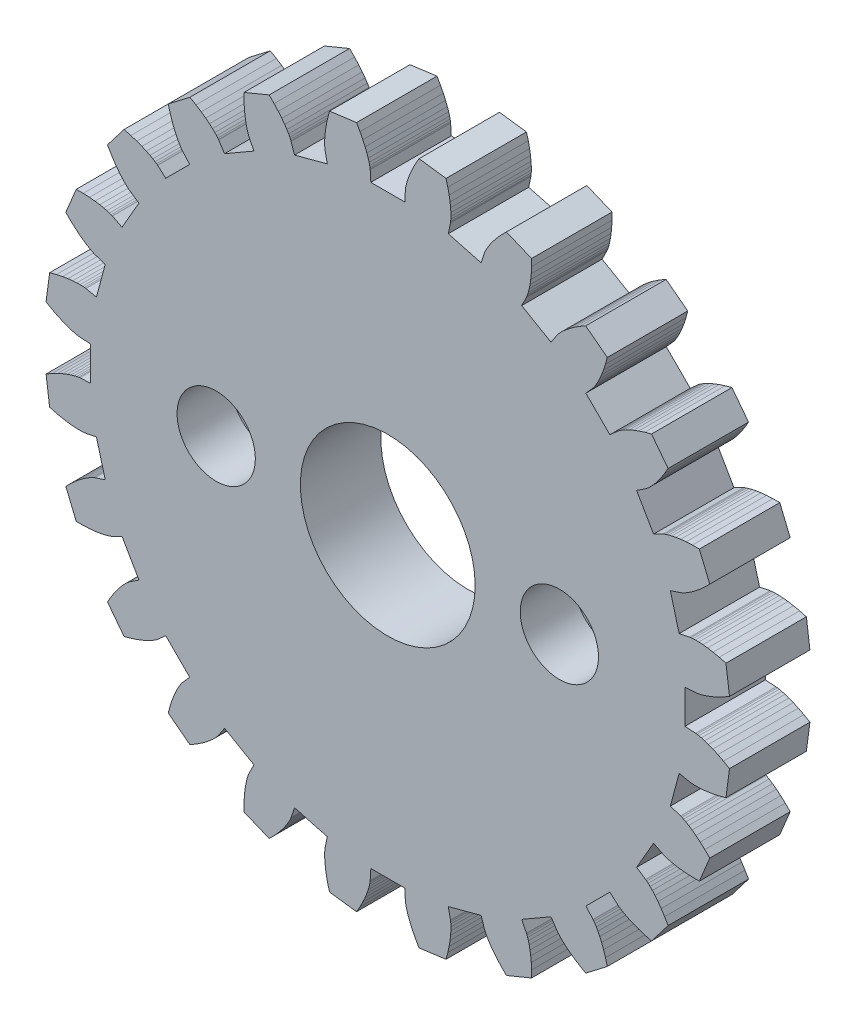
SolidWorks part; units mm, degrees
material "ABS"
ref_plane "Front Plane" through (0, 0, 0) normal (0, 0, 1) x (1, 0, 0)
ref_plane "Top Plane" through (0, 0, 0) normal (0, 1, 0) x (1, 0, 0)
ref_plane "Right Plane" through (0, 0, 0) normal (1, 0, 0) x (0, 0, -1)
sketch "Model" plane through (0, 0, 0) normal (0, 0, 1) x (1, 0, 0)
  line L0 (11.4813, -0.6559) -> (11.0819, -0.6331)
  line L1 (11.0819, -0.6331) -> (11.0819, 0.6331)
  line L2 (11.4813, 0.6559) -> (11.0819, 0.6331)
  line L3 (11.4813, 0.6559) -> (11.495, 0.6571)
  line L4 (11.495, 0.6571) -> (11.5358, 0.6626)
  line L5 (11.5358, 0.6626) -> (11.6033, 0.6749)
  line L6 (11.6033, 0.6749) -> (11.697, 0.6968)
  line L7 (11.697, 0.6968) -> (11.8158, 0.7307)
  line L8 (11.8158, 0.7307) -> (11.9589, 0.7792)
  line L9 (11.9589, 0.7792) -> (12.125, 0.8446)
  line L10 (12.125, 0.8446) -> (12.3128, 0.9294)
  line L11 (12.3128, 0.9294) -> (12.5206, 1.0358)
  line L12 (12.5206, 1.0358) -> (12.7468, 1.1658)
  line L13 (11.2598, 2.338) -> (11.2734, 2.3404)
  line L14 (11.2734, 2.3404) -> (11.3142, 2.3457)
  line L15 (11.3142, 2.3457) -> (11.3827, 2.3512)
  line L16 (11.3827, 2.3512) -> (11.4787, 2.3543)
  line L17 (11.4787, 2.3543) -> (11.6023, 2.3524)
  line L18 (11.6023, 2.3524) -> (11.7531, 2.3426)
  line L19 (11.7531, 2.3426) -> (11.9305, 2.3223)
  line L20 (11.9305, 2.3223) -> (12.1338, 2.289)
  line L21 (12.1338, 2.289) -> (12.362, 2.2401)
  line L22 (12.362, 2.2401) -> (12.6142, 2.173)
  line L23 (12.7468, 1.1658) -> (12.6142, 2.173)
  line L24 (11.2598, 2.338) -> (10.8682, 2.2567)
  line L25 (10.8682, 2.2567) -> (10.5405, 3.4797)
  line L26 (10.9203, 3.6051) -> (10.5405, 3.4797)
  line L27 (10.9203, 3.6051) -> (10.9332, 3.6098)
  line L28 (10.9332, 3.6098) -> (10.9712, 3.6257)
  line L29 (10.9712, 3.6257) -> (11.0333, 3.6551)
  line L30 (11.0333, 3.6551) -> (11.1181, 3.7004)
  line L31 (11.1181, 3.7004) -> (11.2241, 3.764)
  line L32 (11.2241, 3.764) -> (11.3497, 3.8478)
  line L33 (11.3497, 3.8478) -> (11.4933, 3.954)
  line L34 (11.4933, 3.954) -> (11.6527, 4.0845)
  line L35 (11.6527, 4.0845) -> (11.8259, 4.241)
  line L36 (11.8259, 4.241) -> (12.0107, 4.4252)
  line L37 (10.271, 5.1726) -> (10.2835, 5.1784)
  line L38 (10.2835, 5.1784) -> (10.3216, 5.1941)
  line L39 (10.3216, 5.1941) -> (10.3863, 5.2172)
  line L40 (10.3863, 5.2172) -> (10.4783, 5.245)
  line L41 (10.4783, 5.245) -> (10.5981, 5.2751)
  line L42 (10.5981, 5.2751) -> (10.7463, 5.3047)
  line L43 (10.7463, 5.3047) -> (10.9229, 5.331)
  line L44 (10.9229, 5.331) -> (11.1279, 5.3515)
  line L45 (11.1279, 5.3515) -> (11.361, 5.3633)
  line L46 (11.361, 5.3633) -> (11.622, 5.3638)
  line L47 (12.0107, 4.4252) -> (11.622, 5.3638)
  line L48 (10.271, 5.1726) -> (9.9138, 4.9927)
  line L49 (9.9138, 4.9927) -> (9.2807, 6.0892)
  line L50 (9.6151, 6.3087) -> (9.2807, 6.0892)
  line L51 (9.6151, 6.3087) -> (9.6264, 6.3166)
  line L52 (9.6264, 6.3166) -> (9.659, 6.3417)
  line L53 (9.659, 6.3417) -> (9.7113, 6.3862)
  line L54 (9.7113, 6.3862) -> (9.7815, 6.4519)
  line L55 (9.7815, 6.4519) -> (9.8675, 6.5407)
  line L56 (9.8675, 6.5407) -> (9.9671, 6.6542)
  line L57 (9.9671, 6.6542) -> (10.0783, 6.794)
  line L58 (10.0783, 6.794) -> (10.1985, 6.9613)
  line L59 (10.1985, 6.9613) -> (10.3253, 7.1573)
  line L60 (10.3253, 7.1573) -> (10.4561, 7.383)
  line L61 (8.5823, 7.6547) -> (8.5928, 7.6635)
  line L62 (8.5928, 7.6635) -> (8.6256, 7.6885)
  line L63 (8.6256, 7.6885) -> (8.6821, 7.7275)
  line L64 (8.6821, 7.7275) -> (8.7637, 7.7783)
  line L65 (8.7637, 7.7783) -> (8.8717, 7.8384)
  line L66 (8.8717, 7.8384) -> (9.0072, 7.9053)
  line L67 (9.0072, 7.9053) -> (9.1709, 7.9764)
  line L68 (9.1709, 7.9764) -> (9.3636, 8.0492)
  line L69 (9.3636, 8.0492) -> (9.5858, 8.121)
  line L70 (9.5858, 8.121) -> (9.8377, 8.189)
  line L71 (10.4561, 7.383) -> (9.8377, 8.189)
  line L72 (8.5823, 7.6547) -> (8.2838, 7.3885)
  line L73 (8.2838, 7.3885) -> (7.3885, 8.2838)
  line L74 (7.6547, 8.5823) -> (7.3885, 8.2838)
  line L75 (7.6547, 8.5823) -> (7.6635, 8.5928)
  line L76 (7.6635, 8.5928) -> (7.6885, 8.6256)
  line L77 (7.6885, 8.6256) -> (7.7275, 8.6821)
  line L78 (7.7275, 8.6821) -> (7.7783, 8.7637)
  line L79 (7.7783, 8.7637) -> (7.8384, 8.8717)
  line L80 (7.8384, 8.8717) -> (7.9053, 9.0072)
  line L81 (7.9053, 9.0072) -> (7.9764, 9.1709)
  line L82 (7.9764, 9.1709) -> (8.0492, 9.3636)
  line L83 (8.0492, 9.3636) -> (8.121, 9.5858)
  line L84 (8.121, 9.5858) -> (8.189, 9.8377)
  line L85 (6.3087, 9.6151) -> (6.3166, 9.6264)
  line L86 (6.3166, 9.6264) -> (6.3417, 9.659)
  line L87 (6.3417, 9.659) -> (6.3862, 9.7113)
  line L88 (6.3862, 9.7113) -> (6.4519, 9.7815)
  line L89 (6.4519, 9.7815) -> (6.5407, 9.8675)
  line L90 (6.5407, 9.8675) -> (6.6542, 9.9671)
  line L91 (6.6542, 9.9671) -> (6.794, 10.0783)
  line L92 (6.794, 10.0783) -> (6.9613, 10.1985)
  line L93 (6.9613, 10.1985) -> (7.1573, 10.3253)
  line L94 (7.1573, 10.3253) -> (7.383, 10.4561)
  line L95 (8.189, 9.8377) -> (7.383, 10.4561)
  line L96 (6.3087, 9.6151) -> (6.0892, 9.2807)
  line L97 (6.0892, 9.2807) -> (4.9927, 9.9138)
  line L98 (5.1726, 10.271) -> (4.9927, 9.9138)
  line L99 (5.1726, 10.271) -> (5.1784, 10.2835)
  line L100 (5.1784, 10.2835) -> (5.1941, 10.3216)
  line L101 (5.1941, 10.3216) -> (5.2172, 10.3863)
  line L102 (5.2172, 10.3863) -> (5.245, 10.4783)
  line L103 (5.245, 10.4783) -> (5.2751, 10.5981)
  line L104 (5.2751, 10.5981) -> (5.3047, 10.7463)
  line L105 (5.3047, 10.7463) -> (5.331, 10.9229)
  line L106 (5.331, 10.9229) -> (5.3515, 11.1279)
  line L107 (5.3515, 11.1279) -> (5.3633, 11.361)
  line L108 (5.3633, 11.361) -> (5.3638, 11.622)
  line L109 (3.6051, 10.9203) -> (3.6098, 10.9332)
  line L110 (3.6098, 10.9332) -> (3.6257, 10.9712)
  line L111 (3.6257, 10.9712) -> (3.6551, 11.0333)
  line L112 (3.6551, 11.0333) -> (3.7004, 11.1181)
  line L113 (3.7004, 11.1181) -> (3.764, 11.2241)
  line L114 (3.764, 11.2241) -> (3.8478, 11.3497)
  line L115 (3.8478, 11.3497) -> (3.954, 11.4933)
  line L116 (3.954, 11.4933) -> (4.0845, 11.6527)
  line L117 (4.0845, 11.6527) -> (4.241, 11.8259)
  line L118 (4.241, 11.8259) -> (4.4252, 12.0107)
  line L119 (5.3638, 11.622) -> (4.4252, 12.0107)
  line L120 (3.6051, 10.9203) -> (3.4797, 10.5405)
  line L121 (3.4797, 10.5405) -> (2.2567, 10.8682)
  line L122 (2.338, 11.2598) -> (2.2567, 10.8682)
  line L123 (2.338, 11.2598) -> (2.3404, 11.2734)
  line L124 (2.3404, 11.2734) -> (2.3457, 11.3142)
  line L125 (2.3457, 11.3142) -> (2.3512, 11.3827)
  line L126 (2.3512, 11.3827) -> (2.3543, 11.4787)
  line L127 (2.3543, 11.4787) -> (2.3524, 11.6023)
  line L128 (2.3524, 11.6023) -> (2.3426, 11.7531)
  line L129 (2.3426, 11.7531) -> (2.3223, 11.9305)
  line L130 (2.3223, 11.9305) -> (2.289, 12.1338)
  line L131 (2.289, 12.1338) -> (2.2401, 12.362)
  line L132 (2.2401, 12.362) -> (2.173, 12.6142)
  line L133 (0.6559, 11.4813) -> (0.6571, 11.495)
  line L134 (0.6571, 11.495) -> (0.6626, 11.5358)
  line L135 (0.6626, 11.5358) -> (0.6749, 11.6033)
  line L136 (0.6749, 11.6033) -> (0.6968, 11.697)
  line L137 (0.6968, 11.697) -> (0.7307, 11.8158)
  line L138 (0.7307, 11.8158) -> (0.7792, 11.9589)
  line L139 (0.7792, 11.9589) -> (0.8446, 12.125)
  line L140 (0.8446, 12.125) -> (0.9294, 12.3128)
  line L141 (0.9294, 12.3128) -> (1.0358, 12.5206)
  line L142 (1.0358, 12.5206) -> (1.1658, 12.7468)
  line L143 (2.173, 12.6142) -> (1.1658, 12.7468)
  line L144 (0.6559, 11.4813) -> (0.6331, 11.0819)
  line L145 (0.6331, 11.0819) -> (-0.6331, 11.0819)
  line L146 (-0.6559, 11.4813) -> (-0.6331, 11.0819)
  line L147 (-0.6559, 11.4813) -> (-0.6571, 11.495)
  line L148 (-0.6571, 11.495) -> (-0.6626, 11.5358)
  line L149 (-0.6626, 11.5358) -> (-0.6749, 11.6033)
  line L150 (-0.6749, 11.6033) -> (-0.6968, 11.697)
  line L151 (-0.6968, 11.697) -> (-0.7307, 11.8158)
  line L152 (-0.7307, 11.8158) -> (-0.7792, 11.9589)
  line L153 (-0.7792, 11.9589) -> (-0.8446, 12.125)
  line L154 (-0.8446, 12.125) -> (-0.9294, 12.3128)
  line L155 (-0.9294, 12.3128) -> (-1.0358, 12.5206)
  line L156 (-1.0358, 12.5206) -> (-1.1658, 12.7468)
  line L157 (-2.338, 11.2598) -> (-2.3404, 11.2734)
  line L158 (-2.3404, 11.2734) -> (-2.3457, 11.3142)
  line L159 (-2.3457, 11.3142) -> (-2.3512, 11.3827)
  line L160 (-2.3512, 11.3827) -> (-2.3543, 11.4787)
  line L161 (-2.3543, 11.4787) -> (-2.3524, 11.6023)
  line L162 (-2.3524, 11.6023) -> (-2.3426, 11.7531)
  line L163 (-2.3426, 11.7531) -> (-2.3223, 11.9305)
  line L164 (-2.3223, 11.9305) -> (-2.289, 12.1338)
  line L165 (-2.289, 12.1338) -> (-2.2401, 12.362)
  line L166 (-2.2401, 12.362) -> (-2.173, 12.6142)
  line L167 (-1.1658, 12.7468) -> (-2.173, 12.6142)
  line L168 (-2.338, 11.2598) -> (-2.2567, 10.8682)
  line L169 (-2.2567, 10.8682) -> (-3.4797, 10.5405)
  line L170 (-3.6051, 10.9203) -> (-3.4797, 10.5405)
  line L171 (-3.6051, 10.9203) -> (-3.6098, 10.9332)
  line L172 (-3.6098, 10.9332) -> (-3.6257, 10.9712)
  line L173 (-3.6257, 10.9712) -> (-3.6551, 11.0333)
  line L174 (-3.6551, 11.0333) -> (-3.7004, 11.1181)
  line L175 (-3.7004, 11.1181) -> (-3.764, 11.2241)
  line L176 (-3.764, 11.2241) -> (-3.8478, 11.3497)
  line L177 (-3.8478, 11.3497) -> (-3.954, 11.4933)
  line L178 (-3.954, 11.4933) -> (-4.0845, 11.6527)
  line L179 (-4.0845, 11.6527) -> (-4.241, 11.8259)
  line L180 (-4.241, 11.8259) -> (-4.4252, 12.0107)
  line L181 (-5.1726, 10.271) -> (-5.1784, 10.2835)
  line L182 (-5.1784, 10.2835) -> (-5.1941, 10.3216)
  line L183 (-5.1941, 10.3216) -> (-5.2172, 10.3863)
  line L184 (-5.2172, 10.3863) -> (-5.245, 10.4783)
  line L185 (-5.245, 10.4783) -> (-5.2751, 10.5981)
  line L186 (-5.2751, 10.5981) -> (-5.3047, 10.7463)
  line L187 (-5.3047, 10.7463) -> (-5.331, 10.9229)
  line L188 (-5.331, 10.9229) -> (-5.3515, 11.1279)
  line L189 (-5.3515, 11.1279) -> (-5.3633, 11.361)
  line L190 (-5.3633, 11.361) -> (-5.3638, 11.622)
  line L191 (-4.4252, 12.0107) -> (-5.3638, 11.622)
  line L192 (-5.1726, 10.271) -> (-4.9927, 9.9138)
  line L193 (-4.9927, 9.9138) -> (-6.0892, 9.2807)
  line L194 (-6.3087, 9.6151) -> (-6.0892, 9.2807)
  line L195 (-6.3087, 9.6151) -> (-6.3166, 9.6264)
  line L196 (-6.3166, 9.6264) -> (-6.3417, 9.659)
  line L197 (-6.3417, 9.659) -> (-6.3862, 9.7113)
  line L198 (-6.3862, 9.7113) -> (-6.4519, 9.7815)
  line L199 (-6.4519, 9.7815) -> (-6.5407, 9.8675)
  line L200 (-6.5407, 9.8675) -> (-6.6542, 9.9671)
  line L201 (-6.6542, 9.9671) -> (-6.794, 10.0783)
  line L202 (-6.794, 10.0783) -> (-6.9613, 10.1985)
  line L203 (-6.9613, 10.1985) -> (-7.1573, 10.3253)
  line L204 (-7.1573, 10.3253) -> (-7.383, 10.4561)
  line L205 (-7.6547, 8.5823) -> (-7.6635, 8.5928)
  line L206 (-7.6635, 8.5928) -> (-7.6885, 8.6256)
  line L207 (-7.6885, 8.6256) -> (-7.7275, 8.6821)
  line L208 (-7.7275, 8.6821) -> (-7.7783, 8.7637)
  line L209 (-7.7783, 8.7637) -> (-7.8384, 8.8717)
  line L210 (-7.8384, 8.8717) -> (-7.9053, 9.0072)
  line L211 (-7.9053, 9.0072) -> (-7.9764, 9.1709)
  line L212 (-7.9764, 9.1709) -> (-8.0492, 9.3636)
  line L213 (-8.0492, 9.3636) -> (-8.121, 9.5858)
  line L214 (-8.121, 9.5858) -> (-8.189, 9.8377)
  line L215 (-7.383, 10.4561) -> (-8.189, 9.8377)
  line L216 (-7.6547, 8.5823) -> (-7.3885, 8.2838)
  line L217 (-7.3885, 8.2838) -> (-8.2838, 7.3885)
  line L218 (-8.5823, 7.6547) -> (-8.2838, 7.3885)
  line L219 (-8.5823, 7.6547) -> (-8.5928, 7.6635)
  line L220 (-8.5928, 7.6635) -> (-8.6256, 7.6885)
  line L221 (-8.6256, 7.6885) -> (-8.6821, 7.7275)
  line L222 (-8.6821, 7.7275) -> (-8.7637, 7.7783)
  line L223 (-8.7637, 7.7783) -> (-8.8717, 7.8384)
  line L224 (-8.8717, 7.8384) -> (-9.0072, 7.9053)
  line L225 (-9.0072, 7.9053) -> (-9.1709, 7.9764)
  line L226 (-9.1709, 7.9764) -> (-9.3636, 8.0492)
  line L227 (-9.3636, 8.0492) -> (-9.5858, 8.121)
  line L228 (-9.5858, 8.121) -> (-9.8377, 8.189)
  line L229 (-9.6151, 6.3087) -> (-9.6264, 6.3166)
  line L230 (-9.6264, 6.3166) -> (-9.659, 6.3417)
  line L231 (-9.659, 6.3417) -> (-9.7113, 6.3862)
  line L232 (-9.7113, 6.3862) -> (-9.7815, 6.4519)
  line L233 (-9.7815, 6.4519) -> (-9.8675, 6.5407)
  line L234 (-9.8675, 6.5407) -> (-9.9671, 6.6542)
  line L235 (-9.9671, 6.6542) -> (-10.0783, 6.794)
  line L236 (-10.0783, 6.794) -> (-10.1985, 6.9613)
  line L237 (-10.1985, 6.9613) -> (-10.3253, 7.1573)
  line L238 (-10.3253, 7.1573) -> (-10.4561, 7.383)
  line L239 (-9.8377, 8.189) -> (-10.4561, 7.383)
  line L240 (-9.6151, 6.3087) -> (-9.2807, 6.0892)
  line L241 (-9.2807, 6.0892) -> (-9.9138, 4.9927)
  line L242 (-10.271, 5.1726) -> (-9.9138, 4.9927)
  line L243 (-10.271, 5.1726) -> (-10.2835, 5.1784)
  line L244 (-10.2835, 5.1784) -> (-10.3216, 5.1941)
  line L245 (-10.3216, 5.1941) -> (-10.3863, 5.2172)
  line L246 (-10.3863, 5.2172) -> (-10.4783, 5.245)
  line L247 (-10.4783, 5.245) -> (-10.5981, 5.2751)
  line L248 (-10.5981, 5.2751) -> (-10.7463, 5.3047)
  line L249 (-10.7463, 5.3047) -> (-10.9229, 5.331)
  line L250 (-10.9229, 5.331) -> (-11.1279, 5.3515)
  line L251 (-11.1279, 5.3515) -> (-11.361, 5.3633)
  line L252 (-11.361, 5.3633) -> (-11.622, 5.3638)
  line L253 (-10.9203, 3.6051) -> (-10.9332, 3.6098)
  line L254 (-10.9332, 3.6098) -> (-10.9712, 3.6257)
  line L255 (-10.9712, 3.6257) -> (-11.0333, 3.6551)
  line L256 (-11.0333, 3.6551) -> (-11.1181, 3.7004)
  line L257 (-11.1181, 3.7004) -> (-11.2241, 3.764)
  line L258 (-11.2241, 3.764) -> (-11.3497, 3.8478)
  line L259 (-11.3497, 3.8478) -> (-11.4933, 3.954)
  line L260 (-11.4933, 3.954) -> (-11.6527, 4.0845)
  line L261 (-11.6527, 4.0845) -> (-11.8259, 4.241)
  line L262 (-11.8259, 4.241) -> (-12.0107, 4.4252)
  line L263 (-11.622, 5.3638) -> (-12.0107, 4.4252)
  line L264 (-10.9203, 3.6051) -> (-10.5405, 3.4797)
  line L265 (-10.5405, 3.4797) -> (-10.8682, 2.2567)
  line L266 (-11.2598, 2.338) -> (-10.8682, 2.2567)
  line L267 (-11.2598, 2.338) -> (-11.2734, 2.3404)
  line L268 (-11.2734, 2.3404) -> (-11.3142, 2.3457)
  line L269 (-11.3142, 2.3457) -> (-11.3827, 2.3512)
  line L270 (-11.3827, 2.3512) -> (-11.4787, 2.3543)
  line L271 (-11.4787, 2.3543) -> (-11.6023, 2.3524)
  line L272 (-11.6023, 2.3524) -> (-11.7531, 2.3426)
  line L273 (-11.7531, 2.3426) -> (-11.9305, 2.3223)
  line L274 (-11.9305, 2.3223) -> (-12.1338, 2.289)
  line L275 (-12.1338, 2.289) -> (-12.362, 2.2401)
  line L276 (-12.362, 2.2401) -> (-12.6142, 2.173)
  line L277 (-11.4813, 0.6559) -> (-11.495, 0.6571)
  line L278 (-11.495, 0.6571) -> (-11.5358, 0.6626)
  line L279 (-11.5358, 0.6626) -> (-11.6033, 0.6749)
  line L280 (-11.6033, 0.6749) -> (-11.697, 0.6968)
  line L281 (-11.697, 0.6968) -> (-11.8158, 0.7307)
  line L282 (-11.8158, 0.7307) -> (-11.9589, 0.7792)
  line L283 (-11.9589, 0.7792) -> (-12.125, 0.8446)
  line L284 (-12.125, 0.8446) -> (-12.3128, 0.9294)
  line L285 (-12.3128, 0.9294) -> (-12.5206, 1.0358)
  line L286 (-12.5206, 1.0358) -> (-12.7468, 1.1658)
  line L287 (-12.6142, 2.173) -> (-12.7468, 1.1658)
  line L288 (-11.4813, 0.6559) -> (-11.0819, 0.6331)
  line L289 (-11.0819, 0.6331) -> (-11.0819, -0.6331)
  line L290 (-11.4813, -0.6559) -> (-11.0819, -0.6331)
  line L291 (-11.4813, -0.6559) -> (-11.495, -0.6571)
  line L292 (-11.495, -0.6571) -> (-11.5358, -0.6626)
  line L293 (-11.5358, -0.6626) -> (-11.6033, -0.6749)
  line L294 (-11.6033, -0.6749) -> (-11.697, -0.6968)
  line L295 (-11.697, -0.6968) -> (-11.8158, -0.7307)
  line L296 (-11.8158, -0.7307) -> (-11.9589, -0.7792)
  line L297 (-11.9589, -0.7792) -> (-12.125, -0.8446)
  line L298 (-12.125, -0.8446) -> (-12.3128, -0.9294)
  line L299 (-12.3128, -0.9294) -> (-12.5206, -1.0358)
  line L300 (-12.5206, -1.0358) -> (-12.7468, -1.1658)
  line L301 (-11.2598, -2.338) -> (-11.2734, -2.3404)
  line L302 (-11.2734, -2.3404) -> (-11.3142, -2.3457)
  line L303 (-11.3142, -2.3457) -> (-11.3827, -2.3512)
  line L304 (-11.3827, -2.3512) -> (-11.4787, -2.3543)
  line L305 (-11.4787, -2.3543) -> (-11.6023, -2.3524)
  line L306 (-11.6023, -2.3524) -> (-11.7531, -2.3426)
  line L307 (-11.7531, -2.3426) -> (-11.9305, -2.3223)
  line L308 (-11.9305, -2.3223) -> (-12.1338, -2.289)
  line L309 (-12.1338, -2.289) -> (-12.362, -2.2401)
  line L310 (-12.362, -2.2401) -> (-12.6142, -2.173)
  line L311 (-12.7468, -1.1658) -> (-12.6142, -2.173)
  line L312 (-11.2598, -2.338) -> (-10.8682, -2.2567)
  line L313 (-10.8682, -2.2567) -> (-10.5405, -3.4797)
  line L314 (-10.9203, -3.6051) -> (-10.5405, -3.4797)
  line L315 (-10.9203, -3.6051) -> (-10.9332, -3.6098)
  line L316 (-10.9332, -3.6098) -> (-10.9712, -3.6257)
  line L317 (-10.9712, -3.6257) -> (-11.0333, -3.6551)
  line L318 (-11.0333, -3.6551) -> (-11.1181, -3.7004)
  line L319 (-11.1181, -3.7004) -> (-11.2241, -3.764)
  line L320 (-11.2241, -3.764) -> (-11.3497, -3.8478)
  line L321 (-11.3497, -3.8478) -> (-11.4933, -3.954)
  line L322 (-11.4933, -3.954) -> (-11.6527, -4.0845)
  line L323 (-11.6527, -4.0845) -> (-11.8259, -4.241)
  line L324 (-11.8259, -4.241) -> (-12.0107, -4.4252)
  line L325 (-10.271, -5.1726) -> (-10.2835, -5.1784)
  line L326 (-10.2835, -5.1784) -> (-10.3216, -5.1941)
  line L327 (-10.3216, -5.1941) -> (-10.3863, -5.2172)
  line L328 (-10.3863, -5.2172) -> (-10.4783, -5.245)
  line L329 (-10.4783, -5.245) -> (-10.5981, -5.2751)
  line L330 (-10.5981, -5.2751) -> (-10.7463, -5.3047)
  line L331 (-10.7463, -5.3047) -> (-10.9229, -5.331)
  line L332 (-10.9229, -5.331) -> (-11.1279, -5.3515)
  line L333 (-11.1279, -5.3515) -> (-11.361, -5.3633)
  line L334 (-11.361, -5.3633) -> (-11.622, -5.3638)
  line L335 (-12.0107, -4.4252) -> (-11.622, -5.3638)
  line L336 (-10.271, -5.1726) -> (-9.9138, -4.9927)
  line L337 (-9.9138, -4.9927) -> (-9.2807, -6.0892)
  line L338 (-9.6151, -6.3087) -> (-9.2807, -6.0892)
  line L339 (-9.6151, -6.3087) -> (-9.6264, -6.3166)
  line L340 (-9.6264, -6.3166) -> (-9.659, -6.3417)
  line L341 (-9.659, -6.3417) -> (-9.7113, -6.3862)
  line L342 (-9.7113, -6.3862) -> (-9.7815, -6.4519)
  line L343 (-9.7815, -6.4519) -> (-9.8675, -6.5407)
  line L344 (-9.8675, -6.5407) -> (-9.9671, -6.6542)
  line L345 (-9.9671, -6.6542) -> (-10.0783, -6.794)
  line L346 (-10.0783, -6.794) -> (-10.1985, -6.9613)
  line L347 (-10.1985, -6.9613) -> (-10.3253, -7.1573)
  line L348 (-10.3253, -7.1573) -> (-10.4561, -7.383)
  line L349 (-8.5823, -7.6547) -> (-8.5928, -7.6635)
  line L350 (-8.5928, -7.6635) -> (-8.6256, -7.6885)
  line L351 (-8.6256, -7.6885) -> (-8.6821, -7.7275)
  line L352 (-8.6821, -7.7275) -> (-8.7637, -7.7783)
  line L353 (-8.7637, -7.7783) -> (-8.8717, -7.8384)
  line L354 (-8.8717, -7.8384) -> (-9.0072, -7.9053)
  line L355 (-9.0072, -7.9053) -> (-9.1709, -7.9764)
  line L356 (-9.1709, -7.9764) -> (-9.3636, -8.0492)
  line L357 (-9.3636, -8.0492) -> (-9.5858, -8.121)
  line L358 (-9.5858, -8.121) -> (-9.8377, -8.189)
  line L359 (-10.4561, -7.383) -> (-9.8377, -8.189)
  line L360 (-8.5823, -7.6547) -> (-8.2838, -7.3885)
  line L361 (-8.2838, -7.3885) -> (-7.3885, -8.2838)
  line L362 (-7.6547, -8.5823) -> (-7.3885, -8.2838)
  line L363 (-7.6547, -8.5823) -> (-7.6635, -8.5928)
  line L364 (-7.6635, -8.5928) -> (-7.6885, -8.6256)
  line L365 (-7.6885, -8.6256) -> (-7.7275, -8.6821)
  line L366 (-7.7275, -8.6821) -> (-7.7783, -8.7637)
  line L367 (-7.7783, -8.7637) -> (-7.8384, -8.8717)
  line L368 (-7.8384, -8.8717) -> (-7.9053, -9.0072)
  line L369 (-7.9053, -9.0072) -> (-7.9764, -9.1709)
  line L370 (-7.9764, -9.1709) -> (-8.0492, -9.3636)
  line L371 (-8.0492, -9.3636) -> (-8.121, -9.5858)
  line L372 (-8.121, -9.5858) -> (-8.189, -9.8377)
  line L373 (-6.3087, -9.6151) -> (-6.3166, -9.6264)
  line L374 (-6.3166, -9.6264) -> (-6.3417, -9.659)
  line L375 (-6.3417, -9.659) -> (-6.3862, -9.7113)
  line L376 (-6.3862, -9.7113) -> (-6.4519, -9.7815)
  line L377 (-6.4519, -9.7815) -> (-6.5407, -9.8675)
  line L378 (-6.5407, -9.8675) -> (-6.6542, -9.9671)
  line L379 (-6.6542, -9.9671) -> (-6.794, -10.0783)
  line L380 (-6.794, -10.0783) -> (-6.9613, -10.1985)
  line L381 (-6.9613, -10.1985) -> (-7.1573, -10.3253)
  line L382 (-7.1573, -10.3253) -> (-7.383, -10.4561)
  line L383 (-8.189, -9.8377) -> (-7.383, -10.4561)
  line L384 (-6.3087, -9.6151) -> (-6.0892, -9.2807)
  line L385 (-6.0892, -9.2807) -> (-4.9927, -9.9138)
  line L386 (-5.1726, -10.271) -> (-4.9927, -9.9138)
  line L387 (-5.1726, -10.271) -> (-5.1784, -10.2835)
  line L388 (-5.1784, -10.2835) -> (-5.1941, -10.3216)
  line L389 (-5.1941, -10.3216) -> (-5.2172, -10.3863)
  line L390 (-5.2172, -10.3863) -> (-5.245, -10.4783)
  line L391 (-5.245, -10.4783) -> (-5.2751, -10.5981)
  line L392 (-5.2751, -10.5981) -> (-5.3047, -10.7463)
  line L393 (-5.3047, -10.7463) -> (-5.331, -10.9229)
  line L394 (-5.331, -10.9229) -> (-5.3515, -11.1279)
  line L395 (-5.3515, -11.1279) -> (-5.3633, -11.361)
  line L396 (-5.3633, -11.361) -> (-5.3638, -11.622)
  line L397 (-3.6051, -10.9203) -> (-3.6098, -10.9332)
  line L398 (-3.6098, -10.9332) -> (-3.6257, -10.9712)
  line L399 (-3.6257, -10.9712) -> (-3.6551, -11.0333)
  line L400 (-3.6551, -11.0333) -> (-3.7004, -11.1181)
  line L401 (-3.7004, -11.1181) -> (-3.764, -11.2241)
  line L402 (-3.764, -11.2241) -> (-3.8478, -11.3497)
  line L403 (-3.8478, -11.3497) -> (-3.954, -11.4933)
  line L404 (-3.954, -11.4933) -> (-4.0845, -11.6527)
  line L405 (-4.0845, -11.6527) -> (-4.241, -11.8259)
  line L406 (-4.241, -11.8259) -> (-4.4252, -12.0107)
  line L407 (-5.3638, -11.622) -> (-4.4252, -12.0107)
  line L408 (-3.6051, -10.9203) -> (-3.4797, -10.5405)
  line L409 (-3.4797, -10.5405) -> (-2.2567, -10.8682)
  line L410 (-2.338, -11.2598) -> (-2.2567, -10.8682)
  line L411 (-2.338, -11.2598) -> (-2.3404, -11.2734)
  line L412 (-2.3404, -11.2734) -> (-2.3457, -11.3142)
  line L413 (-2.3457, -11.3142) -> (-2.3512, -11.3827)
  line L414 (-2.3512, -11.3827) -> (-2.3543, -11.4787)
  line L415 (-2.3543, -11.4787) -> (-2.3524, -11.6023)
  line L416 (-2.3524, -11.6023) -> (-2.3426, -11.7531)
  line L417 (-2.3426, -11.7531) -> (-2.3223, -11.9305)
  line L418 (-2.3223, -11.9305) -> (-2.289, -12.1338)
  line L419 (-2.289, -12.1338) -> (-2.2401, -12.362)
  line L420 (-2.2401, -12.362) -> (-2.173, -12.6142)
  line L421 (-0.6559, -11.4813) -> (-0.6571, -11.495)
  line L422 (-0.6571, -11.495) -> (-0.6626, -11.5358)
  line L423 (-0.6626, -11.5358) -> (-0.6749, -11.6033)
  line L424 (-0.6749, -11.6033) -> (-0.6968, -11.697)
  line L425 (-0.6968, -11.697) -> (-0.7307, -11.8158)
  line L426 (-0.7307, -11.8158) -> (-0.7792, -11.9589)
  line L427 (-0.7792, -11.9589) -> (-0.8446, -12.125)
  line L428 (-0.8446, -12.125) -> (-0.9294, -12.3128)
  line L429 (-0.9294, -12.3128) -> (-1.0358, -12.5206)
  line L430 (-1.0358, -12.5206) -> (-1.1658, -12.7468)
  line L431 (-2.173, -12.6142) -> (-1.1658, -12.7468)
  line L432 (-0.6559, -11.4813) -> (-0.6331, -11.0819)
  line L433 (-0.6331, -11.0819) -> (0.6331, -11.0819)
  line L434 (0.6559, -11.4813) -> (0.6331, -11.0819)
  line L435 (0.6559, -11.4813) -> (0.6571, -11.495)
  line L436 (0.6571, -11.495) -> (0.6626, -11.5358)
  line L437 (0.6626, -11.5358) -> (0.6749, -11.6033)
  line L438 (0.6749, -11.6033) -> (0.6968, -11.697)
  line L439 (0.6968, -11.697) -> (0.7307, -11.8158)
  line L440 (0.7307, -11.8158) -> (0.7792, -11.9589)
  line L441 (0.7792, -11.9589) -> (0.8446, -12.125)
  line L442 (0.8446, -12.125) -> (0.9294, -12.3128)
  line L443 (0.9294, -12.3128) -> (1.0358, -12.5206)
  line L444 (1.0358, -12.5206) -> (1.1658, -12.7468)
  line L445 (2.338, -11.2598) -> (2.3404, -11.2734)
  line L446 (2.3404, -11.2734) -> (2.3457, -11.3142)
  line L447 (2.3457, -11.3142) -> (2.3512, -11.3827)
  line L448 (2.3512, -11.3827) -> (2.3543, -11.4787)
  line L449 (2.3543, -11.4787) -> (2.3524, -11.6023)
  line L450 (2.3524, -11.6023) -> (2.3426, -11.7531)
  line L451 (2.3426, -11.7531) -> (2.3223, -11.9305)
  line L452 (2.3223, -11.9305) -> (2.289, -12.1338)
  line L453 (2.289, -12.1338) -> (2.2401, -12.362)
  line L454 (2.2401, -12.362) -> (2.173, -12.6142)
  line L455 (1.1658, -12.7468) -> (2.173, -12.6142)
  line L456 (2.338, -11.2598) -> (2.2567, -10.8682)
  line L457 (2.2567, -10.8682) -> (3.4797, -10.5405)
  line L458 (3.6051, -10.9203) -> (3.4797, -10.5405)
  line L459 (3.6051, -10.9203) -> (3.6098, -10.9332)
  line L460 (3.6098, -10.9332) -> (3.6257, -10.9712)
  line L461 (3.6257, -10.9712) -> (3.6551, -11.0333)
  line L462 (3.6551, -11.0333) -> (3.7004, -11.1181)
  line L463 (3.7004, -11.1181) -> (3.764, -11.2241)
  line L464 (3.764, -11.2241) -> (3.8478, -11.3497)
  line L465 (3.8478, -11.3497) -> (3.954, -11.4933)
  line L466 (3.954, -11.4933) -> (4.0845, -11.6527)
  line L467 (4.0845, -11.6527) -> (4.241, -11.8259)
  line L468 (4.241, -11.8259) -> (4.4252, -12.0107)
  line L469 (5.1726, -10.271) -> (5.1784, -10.2835)
  line L470 (5.1784, -10.2835) -> (5.1941, -10.3216)
  line L471 (5.1941, -10.3216) -> (5.2172, -10.3863)
  line L472 (5.2172, -10.3863) -> (5.245, -10.4783)
  line L473 (5.245, -10.4783) -> (5.2751, -10.5981)
  line L474 (5.2751, -10.5981) -> (5.3047, -10.7463)
  line L475 (5.3047, -10.7463) -> (5.331, -10.9229)
  line L476 (5.331, -10.9229) -> (5.3515, -11.1279)
  line L477 (5.3515, -11.1279) -> (5.3633, -11.361)
  line L478 (5.3633, -11.361) -> (5.3638, -11.622)
  line L479 (4.4252, -12.0107) -> (5.3638, -11.622)
  line L480 (5.1726, -10.271) -> (4.9927, -9.9138)
  line L481 (4.9927, -9.9138) -> (6.0892, -9.2807)
  line L482 (6.3087, -9.6151) -> (6.0892, -9.2807)
  line L483 (6.3087, -9.6151) -> (6.3166, -9.6264)
  line L484 (6.3166, -9.6264) -> (6.3417, -9.659)
  line L485 (6.3417, -9.659) -> (6.3862, -9.7113)
  line L486 (6.3862, -9.7113) -> (6.4519, -9.7815)
  line L487 (6.4519, -9.7815) -> (6.5407, -9.8675)
  line L488 (6.5407, -9.8675) -> (6.6542, -9.9671)
  line L489 (6.6542, -9.9671) -> (6.794, -10.0783)
  line L490 (6.794, -10.0783) -> (6.9613, -10.1985)
  line L491 (6.9613, -10.1985) -> (7.1573, -10.3253)
  line L492 (7.1573, -10.3253) -> (7.383, -10.4561)
  line L493 (7.6547, -8.5823) -> (7.6635, -8.5928)
  line L494 (7.6635, -8.5928) -> (7.6885, -8.6256)
  line L495 (7.6885, -8.6256) -> (7.7275, -8.6821)
  line L496 (7.7275, -8.6821) -> (7.7783, -8.7637)
  line L497 (7.7783, -8.7637) -> (7.8384, -8.8717)
  line L498 (7.8384, -8.8717) -> (7.9053, -9.0072)
  line L499 (7.9053, -9.0072) -> (7.9764, -9.1709)
  line L500 (7.9764, -9.1709) -> (8.0492, -9.3636)
  line L501 (8.0492, -9.3636) -> (8.121, -9.5858)
  line L502 (8.121, -9.5858) -> (8.189, -9.8377)
  line L503 (7.383, -10.4561) -> (8.189, -9.8377)
  line L504 (7.6547, -8.5823) -> (7.3885, -8.2838)
  line L505 (7.3885, -8.2838) -> (8.2838, -7.3885)
  line L506 (8.5823, -7.6547) -> (8.2838, -7.3885)
  line L507 (8.5823, -7.6547) -> (8.5928, -7.6635)
  line L508 (8.5928, -7.6635) -> (8.6256, -7.6885)
  line L509 (8.6256, -7.6885) -> (8.6821, -7.7275)
  line L510 (8.6821, -7.7275) -> (8.7637, -7.7783)
  line L511 (8.7637, -7.7783) -> (8.8717, -7.8384)
  line L512 (8.8717, -7.8384) -> (9.0072, -7.9053)
  line L513 (9.0072, -7.9053) -> (9.1709, -7.9764)
  line L514 (9.1709, -7.9764) -> (9.3636, -8.0492)
  line L515 (9.3636, -8.0492) -> (9.5858, -8.121)
  line L516 (9.5858, -8.121) -> (9.8377, -8.189)
  line L517 (9.6151, -6.3087) -> (9.6264, -6.3166)
  line L518 (9.6264, -6.3166) -> (9.659, -6.3417)
  line L519 (9.659, -6.3417) -> (9.7113, -6.3862)
  line L520 (9.7113, -6.3862) -> (9.7815, -6.4519)
  line L521 (9.7815, -6.4519) -> (9.8675, -6.5407)
  line L522 (9.8675, -6.5407) -> (9.9671, -6.6542)
  line L523 (9.9671, -6.6542) -> (10.0783, -6.794)
  line L524 (10.0783, -6.794) -> (10.1985, -6.9613)
  line L525 (10.1985, -6.9613) -> (10.3253, -7.1573)
  line L526 (10.3253, -7.1573) -> (10.4561, -7.383)
  line L527 (9.8377, -8.189) -> (10.4561, -7.383)
  line L528 (9.6151, -6.3087) -> (9.2807, -6.0892)
  line L529 (9.2807, -6.0892) -> (9.9138, -4.9927)
  line L530 (10.271, -5.1726) -> (9.9138, -4.9927)
  line L531 (10.271, -5.1726) -> (10.2835, -5.1784)
  line L532 (10.2835, -5.1784) -> (10.3216, -5.1941)
  line L533 (10.3216, -5.1941) -> (10.3863, -5.2172)
  line L534 (10.3863, -5.2172) -> (10.4783, -5.245)
  line L535 (10.4783, -5.245) -> (10.5981, -5.2751)
  line L536 (10.5981, -5.2751) -> (10.7463, -5.3047)
  line L537 (10.7463, -5.3047) -> (10.9229, -5.331)
  line L538 (10.9229, -5.331) -> (11.1279, -5.3515)
  line L539 (11.1279, -5.3515) -> (11.361, -5.3633)
  line L540 (11.361, -5.3633) -> (11.622, -5.3638)
  line L541 (10.9203, -3.6051) -> (10.9332, -3.6098)
  line L542 (10.9332, -3.6098) -> (10.9712, -3.6257)
  line L543 (10.9712, -3.6257) -> (11.0333, -3.6551)
  line L544 (11.0333, -3.6551) -> (11.1181, -3.7004)
  line L545 (11.1181, -3.7004) -> (11.2241, -3.764)
  line L546 (11.2241, -3.764) -> (11.3497, -3.8478)
  line L547 (11.3497, -3.8478) -> (11.4933, -3.954)
  line L548 (11.4933, -3.954) -> (11.6527, -4.0845)
  line L549 (11.6527, -4.0845) -> (11.8259, -4.241)
  line L550 (11.8259, -4.241) -> (12.0107, -4.4252)
  line L551 (11.622, -5.3638) -> (12.0107, -4.4252)
  line L552 (10.9203, -3.6051) -> (10.5405, -3.4797)
  line L553 (10.5405, -3.4797) -> (10.8682, -2.2567)
  line L554 (11.2598, -2.338) -> (10.8682, -2.2567)
  line L555 (11.2598, -2.338) -> (11.2734, -2.3404)
  line L556 (11.2734, -2.3404) -> (11.3142, -2.3457)
  line L557 (11.3142, -2.3457) -> (11.3827, -2.3512)
  line L558 (11.3827, -2.3512) -> (11.4787, -2.3543)
  line L559 (11.4787, -2.3543) -> (11.6023, -2.3524)
  line L560 (11.6023, -2.3524) -> (11.7531, -2.3426)
  line L561 (11.7531, -2.3426) -> (11.9305, -2.3223)
  line L562 (11.9305, -2.3223) -> (12.1338, -2.289)
  line L563 (12.1338, -2.289) -> (12.362, -2.2401)
  line L564 (12.362, -2.2401) -> (12.6142, -2.173)
  line L565 (11.4813, -0.6559) -> (11.495, -0.6571)
  line L566 (11.495, -0.6571) -> (11.5358, -0.6626)
  line L567 (11.5358, -0.6626) -> (11.6033, -0.6749)
  line L568 (11.6033, -0.6749) -> (11.697, -0.6968)
  line L569 (11.697, -0.6968) -> (11.8158, -0.7307)
  line L570 (11.8158, -0.7307) -> (11.9589, -0.7792)
  line L571 (11.9589, -0.7792) -> (12.125, -0.8446)
  line L572 (12.125, -0.8446) -> (12.3128, -0.9294)
  line L573 (12.3128, -0.9294) -> (12.5206, -1.0358)
  line L574 (12.5206, -1.0358) -> (12.7468, -1.1658)
  line L575 (12.6142, -2.173) -> (12.7468, -1.1658)
extrude "Main Gear Body" add sketch "Model" along normal blind 3
scale "Scale1" scale about centroid uniform scaling yes scale factor 1.25
sketch "Sketch1" plane through (0, 0, 3.375) normal (0, 0, 1) x (1, 0, 0)
  line L0 (-8, 0) -> (8, 0) construction
  circle A0 centre (0, 0) radius 4.075
  circle A1 centre (-8, 0) radius 1.15
  circle A2 centre (8, 0) radius 1.15
  dimension "D1" = 16
  dimension "D2" = 2.3
  dimension "D3" = 8.15
extrude "Servo Clearance" cut sketch "Sketch1" against normal through all
sketch "Sketch2" plane through (0, 0, 3.375) normal (0, 0, 1) x (1, 0, 0)
  circle A0 centre (8, 0) radius 1.825
  circle A1 centre (-8, 0) radius 1.825
  circle A3 centre (-8, 0) radius 1.15 construction
  circle A4 centre (8, 0) radius 1.15 construction
  dimension "D1" = 3.65
extrude "Bolt Head Clearance" cut sketch "Sketch2" against normal blind 2.5
ref_point "Point1"
